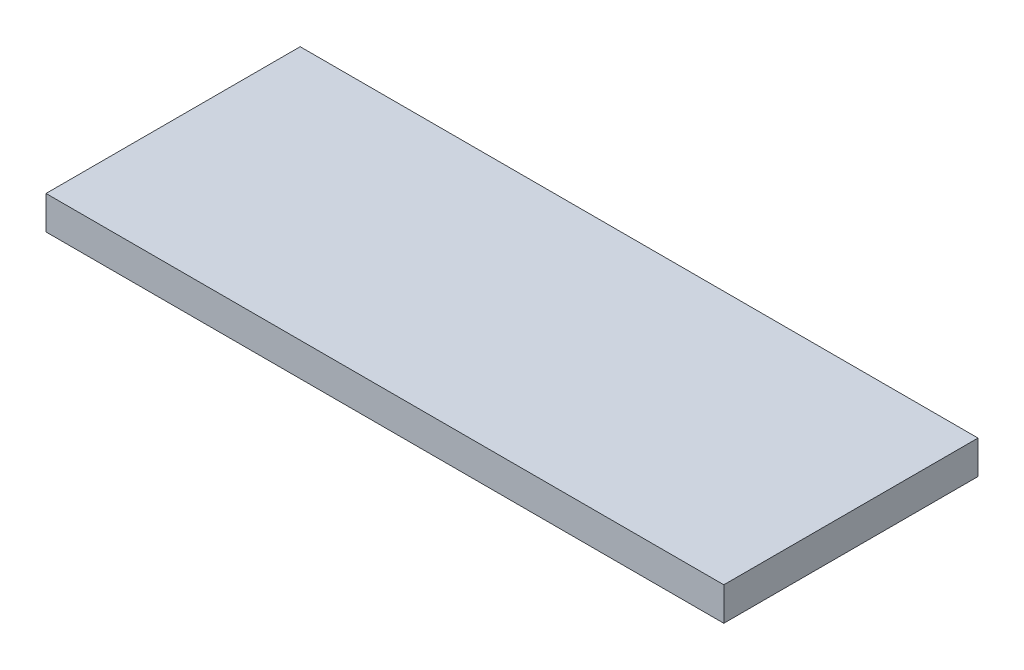
SolidWorks part; units mm, degrees
material "Cedar"
ref_plane "Front Plane" through (0, 0, 0) normal (0, 0, 1) x (1, 0, 0)
ref_plane "Top Plane" through (0, 0, 0) normal (0, 1, 0) x (1, 0, 0)
ref_plane "Right Plane" through (0, 0, 0) normal (1, 0, 0) x (0, 0, -1)
sketch "Main Base Dim" plane through (0, 0, 0) normal (0, 1, 0) x (1, 0, 0)
  line L1 (0, 0) -> (406.4, 0)
  line L2 (0, 0) -> (0, 152.4)
  line L3 (0, 152.4) -> (406.4, 152.4)
  line L4 (406.4, 0) -> (406.4, 152.4)
  dimension "D1" = 152.4
  dimension "D2" = 406.4
extrude "Main Base" add sketch "Main Base Dim" along normal blind 20
